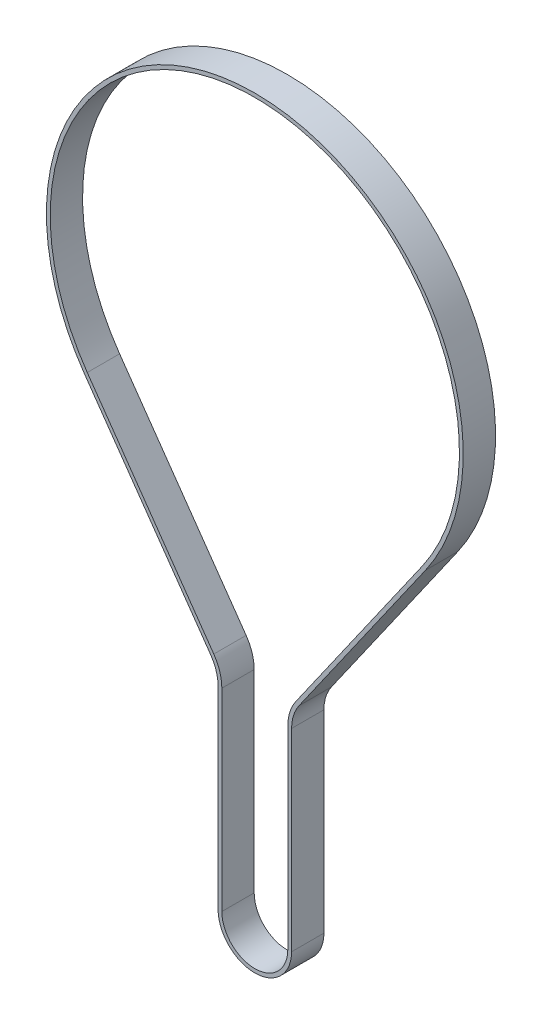
SolidWorks part; units mm, degrees
material "Rubber"
ref_plane "Front Plane" through (0, 0, 0) normal (0, 0, 1) x (1, 0, 0)
ref_plane "Top Plane" through (0, 0, 0) normal (0, 1, 0) x (1, 0, 0)
ref_plane "Right Plane" through (0, 0, 0) normal (1, 0, 0) x (0, 0, -1)
sketch "Sketch1" plane through (0, 0, 0) normal (0, 0, 1) x (1, 0, 0)
  line L10 (-6.3662, 0) -> (-6.3662, 35.8707)
  line L11 (-7.8146, 40.4616) -> (-31.2815, 73.9506)
  line L12 (31.2815, 73.9506) -> (7.8146, 40.4616)
  line L13 (6.3662, 35.8707) -> (6.3662, 0)
  arc A6 (-31.2815, 73.9506) -> (31.2815, 73.9506) centre (0, 95.8707) cw
  arc A7 (-6.3662, 0) -> (6.3662, 0) centre (0, 0) ccw
  arc A8 (-6.3662, 35.8707) -> (-7.8146, 40.4616) centre (-14.3662, 35.8707) ccw
  arc A9 (7.8146, 40.4616) -> (6.3662, 35.8707) centre (14.3662, 35.8707) ccw
  point P0 (0, 0)
  dimension "D8" = 8
  dimension "D9" = 6.3662
  dimension "D10" = 38.1972
  dimension "D3" = 60
  dimension "D2" = 350
sketch "Sketch2" plane through (0, 0, 0) normal (0, 0, 1) x (1, 0, 0)
  line L20 (-6.8162, 35.8707) -> (-6.8162, 0)
  line L21 (6.8162, 0) -> (6.8162, 35.8707)
  line L22 (8.1831, 40.2034) -> (31.6501, 73.6923)
  line L23 (-31.6501, 73.6923) -> (-8.1831, 40.2034)
  line L24 (-6.1162, 35.8707) -> (-6.1162, 0)
  line L25 (6.1162, 0) -> (6.1162, 35.8707)
  line L26 (7.6099, 40.6051) -> (31.0768, 74.0941)
  line L27 (-31.0768, 74.0941) -> (-7.6099, 40.6051)
  line L28 (-6.1162, 35.8707) -> (-6.1162, 0)
  line L29 (6.1162, 0) -> (6.1162, 35.8707)
  line L30 (7.6099, 40.6051) -> (31.0768, 74.0941)
  line L31 (-31.0768, 74.0941) -> (-7.6099, 40.6051)
  arc A16 (-6.8162, 0) -> (6.8162, 0) centre (0, 0) ccw
  arc A17 (8.1831, 40.2034) -> (6.8162, 35.8707) centre (14.3662, 35.8707) ccw
  arc A18 (31.6501, 73.6923) -> (-31.6501, 73.6923) centre (0, 95.8707) ccw
  arc A19 (-6.8162, 35.8707) -> (-8.1831, 40.2034) centre (-14.3662, 35.8707) ccw
  arc A20 (-6.1162, 35.8707) -> (-7.6099, 40.6051) centre (-14.3662, 35.8707) ccw
  arc A21 (-6.1162, 0) -> (6.1162, 0) centre (0, 0) ccw
  arc A22 (7.6099, 40.6051) -> (6.1162, 35.8707) centre (14.3662, 35.8707) ccw
  arc A23 (31.0768, 74.0941) -> (-31.0768, 74.0941) centre (0, 95.8707) ccw
  arc A24 (-6.1162, 35.8707) -> (-7.6099, 40.6051) centre (-14.3662, 35.8707) ccw
  arc A25 (-6.1162, 0) -> (6.1162, 0) centre (0, 0) ccw
  arc A26 (7.6099, 40.6051) -> (6.1162, 35.8707) centre (14.3662, 35.8707) ccw
  arc A27 (31.0768, 74.0941) -> (-31.0768, 74.0941) centre (0, 95.8707) ccw
  dimension "D1" = 0.25
  dimension "D2" = 0.7
extrude "Boss-Extrude1" add sketch "Sketch2" along normal blind 6
